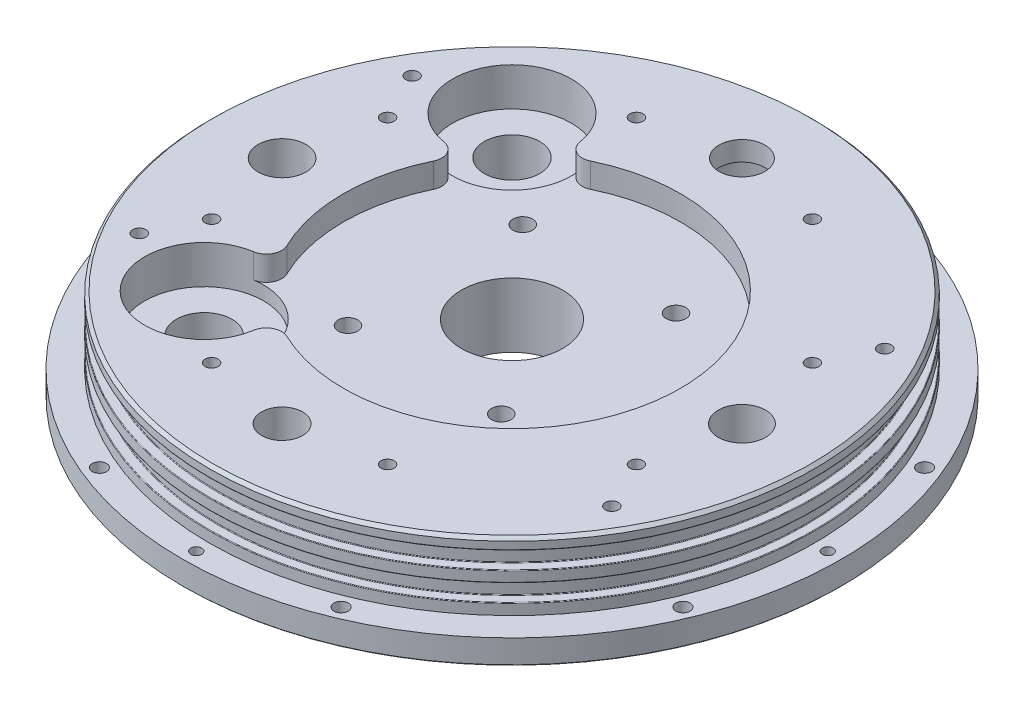
SolidWorks part; units mm, degrees
other "Markup1"
sketch "Sketch44" plane through (68.2625, -5.08, 68.2625) normal (0.274, -0.9578, 0.0865) x (-0.9537, -0.259, 0.1532)
material "6061-T6 (SS)"
ref_plane "Front Plane" through (0, 0, 0) normal (0, 0, 1) x (1, 0, 0)
ref_plane "Top Plane" through (0, 0, 0) normal (0, 1, 0) x (1, 0, 0)
ref_plane "Right Plane" through (0, 0, 0) normal (1, 0, 0) x (0, 0, -1)
ref_plane "Plane1" through (0, -5.08, 0) normal (0, -1, 0) x (1, 0, 0)
sketch "Sketch1" plane through (0, -5.08, 0) normal (0, -1, 0) x (1, 0, 0)
  circle A0 centre (0, 0) radius 68.2625
  dimension "D1" = 136.525
extrude "Boss-Extrude1" add sketch "Sketch1" against normal blind 19.05
sketch "Sketch2" plane through (0, -5.08, 0) normal (0, -1, 0) x (1, 0, 0)
  line L0 (0, 0) -> (0, -47.625) construction
  line L1 (0, 0) -> (25.4, 0) construction
  circle A0 centre (0, -47.625) radius 11.65
  dimension "D3" = 23.3
  dimension "D1" = 90
  dimension "D2" = 47.625
extrude "Cut-Extrude1" cut sketch "Sketch2" against normal blind 1.5
hole_wizard "M22x1.0 Tapped Hole2" positions "Sketch4" profile "Sketch3" tap size "M22x1.0" standard "ANSI Metric"
sketch "Sketch4" plane through (0, -3.58, 0) normal (0, -1, 0) x (-1, 0, 0)
  line L0 (0, 0) -> (0, 47.625) construction
  point P0 (0, 47.625)
  dimension "D1" = 47.625
sketch "Sketch3" plane through (0, -3.58, -47.625) normal (1, 0, 0) x (0, 0, -1)
  line L0 (0, 0) -> (0, 3.5001)
  line L1 (0, 3.5001) -> (10.325, 3.5001)
  line L2 (10.325, 3.5001) -> (10.325, 0)
  line L5 (10.325, 0) -> (0, 0)
  line L10 (0, 3.5001) -> (-10.325, 3.5001) construction
  line L11 (0, -6.35) -> (0, 107.95) construction
  dimension "Tap Drill Dia." = 20.65
  dimension "Tap Drill Depth" = 3.5001
  dimension "Drill Angle" = 180
cosmetic thread "Hole Thread16" parameters "D1"=3.5001, "D2"=22
sketch "Sketch5" plane through (0, -0.0799, 0) normal (0, -1, 0) x (1, 0, 0)
  line L0 (0, 0) -> (0, -47.625) construction
  circle A0 centre (0, -47.625) radius 10.325
  dimension "D1" = 20.65
extrude "Cut-Extrude2" cut sketch "Sketch5" against normal blind 1.4
sketch "Sketch6" plane through (0, 1.3201, 0) normal (0, -1, 0) x (1, 0, 0)
  line L0 (0, 0) -> (0, -47.625) construction
  circle A0 centre (0, -47.625) radius 9.65
  dimension "D1" = 19.3
extrude "Cut-Extrude3" cut sketch "Sketch6" against normal blind 0.9
ref_plane "Plane2" through (0, 2.22, 0) normal (0, -1, 0) x (1, 0, 0)
sketch "Sketch7" plane through (0, 2.22, 0) normal (0, -1, 0) x (1, 0, 0)
  circle A0 centre (0, -47.625) radius 10.1
  dimension "D1" = 20.2
extrude "Cut-Extrude4" cut sketch "Sketch7" against normal blind 1.2
sketch "Sketch8" plane through (0, 3.42, 0) normal (0, -1, 0) x (1, 0, 0)
  circle A0 centre (0, -47.625) radius 9.515
  dimension "D1" = 19.03
extrude "Cut-Extrude5" cut sketch "Sketch8" against normal blind 5
chamfer "Chamfer1" distance 0.4346 angle 49 1 edges at (0, 3.42, -38.11)
sketch "Sketch9" plane through (0, 8.42, 0) normal (0, -1, 0) x (1, 0, 0)
  line L0 (0, 0) -> (0, -47.625) construction
  circle A0 centre (0, -47.625) radius 7.5
  dimension "D1" = 15
extrude "Cut-Extrude6" cut sketch "Sketch9" against normal blind 1.5
ref_plane "Plane3" through (0, 0, 0) normal (-0.7071, 0, 0.7071) x (0, -1, 0)
sketch "Sketch10" plane through (0, 0, 0) normal (-0.7071, 0, 0.7071) x (0, -1, 0)
  line L0 (0, 68.3133) -> (-13.97, 68.3133)
  line L1 (-13.97, 68.3133) -> (-13.97, 62.5983)
  line L2 (-13.97, 62.5983) -> (0, 62.5983)
  line L3 (0, 62.5983) -> (0, 68.3133)
  line L4 (0, 0) -> (-13.97, 0) construction
  line L5 (-13.97, 0) -> (-13.97, 62.5983) construction
  dimension "D1" = 62.5983
  dimension "D2" = 5.715
  dimension "D3" = 13.97
  dimension "D4" = 13.97
revolve "Cut-Revolve1" cut sketch "Sketch10" angle 360 about L4
hole_wizard "#4 Clearance Hole1" positions "Sketch12" profile "Sketch11" hole size "#4" standard "ANSI Inch" end condition through all
sketch "Sketch12" plane through (0, -5.08, 0) normal (0, -1, 0) x (-1, 0, 0)
  line L0 (0, 0) -> (25.0294, -60.4263) construction
  line L2 (0, 0) -> (-25.0294, -60.4263) construction
  line L4 (0, 0) -> (-60.4263, -25.0294) construction
  line L6 (0, 0) -> (-60.4263, 25.0294) construction
  line L8 (0, 0) -> (-25.0294, 60.4263) construction
  line L10 (0, 0) -> (25.0294, 60.4263) construction
  line L12 (0, 0) -> (60.4263, 25.0294) construction
  line L14 (0, 0) -> (60.4263, -25.0294) construction
  line L16 (0, 0) -> (0, 65.405) construction
  circle A1 centre (0, 0) radius 65.405 construction
  point P0 (25.0294, -60.4263)
  point P1 (25.0294, 60.4263)
  point P2 (60.4263, -25.0294)
  point P3 (-25.0294, 60.4263)
  point P4 (-60.4263, 25.0294)
  point P5 (-60.4263, -25.0294)
  point P6 (-25.0294, -60.4263)
  point P7 (60.4263, 25.0294)
  point P57 (0, 0)
  point P58 (0, 0)
  point P59 (0, 0)
  point P60 (0, 0)
  point P61 (0, 0)
  point P62 (0, 0)
  point P63 (0, 0)
  point P64 (0, 0)
  point P65 (0, 0)
  point P66 (0, 0)
  dimension "D1" = 130.81
  dimension "D2" = 22.5
  dimension "D3" = 22.5
  dimension "D4" = 45
sketch "Sketch11" plane through (-25.0294, -5.08, 60.4263) normal (1, 0, 0) x (0, 0, -1)
  line L0 (0, 0) -> (0, 19.05)
  line L1 (0, 19.05) -> (1.4732, 19.05)
  line L2 (1.4732, 19.05) -> (1.4732, 0)
  line L5 (1.4732, 0) -> (0, 0)
  line L11 (0, -6.35) -> (0, 107.95) construction
  dimension "Thru Hole Dia." = 2.9464
  dimension "Thru Hole Depth" = 19.05
hole_wizard "#4-40 Tapped Hole1" positions "Sketch14" profile "Sketch13" tap size "#4-40" standard "ANSI Inch" end condition through all
sketch "Sketch14" plane through (0, -5.08, 0) normal (0, -1, 0) x (-1, 0, 0)
  line L0 (0, 0) -> (0, 65.405) construction
  line L2 (0, 0) -> (65.405, 0) construction
  line L3 (0, 0) -> (0, -65.405) construction
  line L4 (0, 0) -> (-65.405, 0) construction
  circle A0 centre (0, 0) radius 65.405 construction
  point P0 (0, -65.405)
  point P1 (0, 65.405)
  point P2 (-65.405, 0)
  point P3 (65.405, 0)
  point P20 (0, 0)
  point P21 (0, 0)
  point P22 (0, 0)
  point P23 (0, 0)
  point P24 (0, 0)
  point P25 (0.0664, 65.405)
  point P26 (0.1049, 65.405)
  point P27 (0, 0)
  point P28 (0, 0)
  point P29 (0, 0)
  point P30 (0.0003, 65.405)
  point P31 (0.0019, 65.405)
  point P32 (0, 65.405)
  point P33 (0, 0)
  point P34 (0, 0)
  point P35 (0, 65.405)
  dimension "D2" = 130.81
  dimension "D1" = 4
sketch "Sketch13" plane through (0, -5.08, 65.405) normal (1, 0, 0) x (0, 0, -1)
  line L0 (0, 0) -> (0, 19.05)
  line L1 (0, 19.05) -> (1.1303, 19.05)
  line L2 (1.1303, 19.05) -> (1.1303, 0)
  line L5 (1.1303, 0) -> (0, 0)
  line L11 (0, -6.35) -> (0, 107.95) construction
  dimension "Thru Tap Drill Dia." = 2.2606
  dimension "Thru Tap Drill Depth" = 19.05
cosmetic thread "Hole Thread21" parameters "D2"=2.8448
cosmetic thread "Hole Thread22" parameters "D2"=2.8448
cosmetic thread "Hole Thread23" parameters "D2"=2.8448
cosmetic thread "Hole Thread24" parameters "D2"=2.8448
hole_wizard "Hole2" positions "Sketch16" profile "Sketch15" legacy end condition through all
sketch "Sketch16" plane through (0, 9.92, 0) normal (0, -1, 0) x (-1, 0, 0)
  line L0 (0, 0) -> (0, 47.625) construction
  point P0 (0, 47.625)
sketch "Sketch15" plane through (0, 9.92, -47.625) normal (1, 0, 0) x (0, 0, -1)
  line L0 (0, 0) -> (0, 4.05)
  line L1 (0, 4.05) -> (4.75, 4.05)
  line L2 (4.75, 4.05) -> (4.75, 0)
  line L3 (4.75, 0) -> (0, 0)
  line L4 (0, 110) -> (0, -10) construction
  dimension "Diameter" = 9.5
  dimension "Depth" = 4.05
sketch "Sketch40" plane through (0, 13.97, 0) normal (0, 1, 0) x (1, 0, 0)
  line L0 (0, 0) -> (-56.515, 0) construction
  line L1 (48.9434, -28.2575) -> (-48.9434, 28.2575)
  line L2 (-48.9434, -28.2575) -> (48.9434, 28.2575)
  circle A0 centre (0, 0) radius 56.515
  point P7 (0, 0)
  point P10 (0, 0)
  dimension "D1" = 113.03
  dimension "D2" = 30
  dimension "D3" = 30
hole_wizard "M10x1.5 Tapped Hole2" positions "Sketch22" profile "Sketch21" tap size "M10x1.5" standard "ANSI Metric" end condition up to next
sketch "Sketch22" plane through (0, -5.08, 0) normal (0, -1, 0) x (-1, 0, 0)
  line L0 (0, 0) -> (0, -47.625)
  point P0 (0, -47.625)
  dimension "D1" = 47.625
cosmetic thread "Hole Thread13" parameters "D2"=10
sketch "Sketch21" plane through (0, -5.08, 47.625) normal (1, 0, 0) x (0, 0, -1)
  line L0 (0, 0) -> (0, 19.05)
  line L1 (0, 19.05) -> (4.25, 19.05)
  line L2 (4.25, 19.05) -> (4.25, 0)
  line L5 (4.25, 0) -> (0, 0)
  line L11 (0, -6.35) -> (0, 107.95) construction
  dimension "Thru Tap Drill Dia." = 8.5
  dimension "Thru Tap Drill Depth" = 19.05
hole_wizard "Hole4" positions "Sketch24" profile "Sketch23" legacy end condition through all
sketch "Sketch24" plane through (0, -5.08, 0) normal (0, -1, 0) x (-1, 0, 0)
  line L0 (0, 0) -> (-47.625, 0)
  point P0 (-47.625, 0)
  dimension "D1" = 47.625
sketch "Sketch23" plane through (47.625, -5.08, 0) normal (1, 0, 0) x (0, 0, -1)
  line L0 (0, 0) -> (0, 19.05)
  line L1 (0, 19.05) -> (4.9, 19.05)
  line L2 (4.9, 19.05) -> (4.9, 0)
  line L3 (4.9, 0) -> (0, 0)
  line L4 (0, 110) -> (0, -10) construction
  dimension "Diameter" = 9.8
  dimension "Depth" = 19.05
hole_wizard "7/8-20 Tapped Hole1" positions "Sketch26" profile "Sketch25" tap size "7/8-20" standard "ANSI Inch" end condition up to next
sketch "Sketch26" plane through (0, -5.08, 0) normal (0, -1, 0) x (-1, 0, 0)
  point P0 (0, 0)
cosmetic thread "Hole Thread14" parameters "D2"=22.225
sketch "Sketch25" plane through (0, -5.08, 0) normal (1, 0, 0) x (0, 0, -1)
  line L0 (0, 0) -> (0, 19.05)
  line L1 (0, 19.05) -> (10.4902, 19.05)
  line L2 (10.4902, 19.05) -> (10.4902, 0)
  line L5 (10.4902, 0) -> (0, 0)
  line L11 (0, -6.35) -> (0, 107.95) construction
  dimension "Thru Tap Drill Dia." = 20.9804
  dimension "Thru Tap Drill Depth" = 19.05
hole_wizard "7/16-20 Tapped Hole1" positions "Sketch28" profile "Sketch27" tap size "7/16-20" standard "ANSI Inch" end condition through all
sketch "Sketch28" plane through (0, -5.08, 0) normal (0, -1, 0) x (-1, 0, 0)
  line L0 (0, 0) -> (47.625, 0) construction
  point P0 (47.625, 0)
  dimension "D1" = 47.625
sketch "Sketch27" plane through (-47.625, -5.08, 0) normal (1, 0, 0) x (0, 0, -1)
  line L0 (0, 0) -> (0, 19.05)
  line L1 (0, 19.05) -> (4.9606, 19.05)
  line L2 (4.9606, 19.05) -> (4.9606, 0)
  line L5 (4.9606, 0) -> (0, 0)
  line L11 (0, -6.35) -> (0, 107.95) construction
  dimension "Thru Tap Drill Dia." = 9.9212
  dimension "Thru Tap Drill Depth" = 19.05
cosmetic thread "Hole Thread15" parameters "D2"=11.1125
hole_wizard "7/16 Clearance Hole1" positions "Sketch30" profile "Sketch29" hole size "7/16" standard "ANSI Inch" end condition through all
sketch "Sketch30" plane through (0, 13.97, 0) normal (0, 1, 0) x (1, 0, 0)
  line L0 (0, 0) -> (-31.8799, 31.8799)
  line L2 (0, 0) -> (-31.8799, -31.8799)
  line L4 (0, 0) -> (-45.085, 0)
  point P0 (-31.8799, 31.8799)
  point P1 (-31.8799, -31.8799)
  dimension "D1" = 45.085
  dimension "D2" = 90
  dimension "D3" = 45
sketch "Sketch29" plane through (-31.8799, 13.97, -31.8799) normal (1, 0, 0) x (0, 0, 1)
  line L0 (0, 0) -> (0, 19.05)
  line L1 (0, 19.05) -> (5.755, 19.05)
  line L2 (5.755, 19.05) -> (5.755, 0)
  line L5 (5.755, 0) -> (0, 0)
  line L11 (0, -6.35) -> (0, 107.95) construction
  dimension "Thru Hole Dia." = 11.51
  dimension "Thru Hole Depth" = 19.05
sketch "Sketch31" plane through (0, 13.97, 0) normal (0, 1, 0) x (-1, 0, 0)
  line L0 (31.8799, -31.8799) -> (0, 0) construction
  line L1 (0, 0) -> (31.8799, 31.8799) construction
  line L2 (0, 0) -> (47.625, 0) construction
  circle A1 centre (31.8799, -31.8799) radius 12.319
  circle A2 centre (31.8799, 31.8799) radius 5.755 construction
  circle A3 centre (31.8799, 31.8799) radius 12.319
  circle A4 centre (31.8799, -31.8799) radius 5.755 construction
  dimension "D1" = 24.638
  dimension "D2" = 24.638
extrude "Cut-Extrude7" cut sketch "Sketch31" against normal blind 7.9375
sketch "Sketch32" plane through (0, -5.08, 0) normal (0, -1, 0) x (1, 0, 0)
  line L0 (0, 0) -> (47.625, 0) construction
  circle A0 centre (47.625, 0) radius 4.7625
  circle A1 centre (47.625, 0) radius 7.1374
  dimension "D1" = 14.2748
  dimension "D2" = 9.525
  dimension "D3" = 47.625
extrude "Cut-Extrude8" cut sketch "Sketch32" against normal blind 7.62
sketch "Sketch33" plane through (0, -5.08, 0) normal (0, -1, 0) x (1, 0, 0)
  line L0 (47.625, 0) -> (0, 0) construction
  line L2 (-31.8799, 31.8799) -> (0, 0) construction
  line L3 (0, 0) -> (-47.625, 0) construction
  line L4 (-31.8799, -31.8799) -> (0, 0) construction
  line L5 (0, 0) -> (0, 47.625) construction
  circle A0 centre (47.625, 0) radius 6.35
  circle A1 centre (47.625, 0) radius 13.6525
  circle A2 centre (0, 47.625) radius 2.54
  circle A3 centre (0, 47.625) radius 11.1125
  circle A4 centre (-31.8799, -31.8799) radius 5.08
  circle A5 centre (-31.8799, -31.8799) radius 10.4775
  circle A6 centre (-47.625, 0) radius 4.7625
  circle A7 centre (-47.625, 0) radius 15.24
  circle A8 centre (-31.8799, 31.8799) radius 5.08
  circle A9 centre (-31.8799, 31.8799) radius 10.4775
  circle A10 centre (0, 0) radius 5.7341
  circle A11 centre (0, 0) radius 24.4475
  circle A12 centre (0, 0) radius 47.625 construction
  dimension "D1" = 27.305
  dimension "D2" = 48.895
  dimension "D3" = 20.955
  dimension "D4" = 30.48
  dimension "D5" = 20.955
  dimension "D6" = 22.225
  dimension "D7" = 95.25
  dimension "D11" = 5.08
  dimension "D12" = 10.16
  dimension "D13" = 9.525
  dimension "D14" = 10.16
  dimension "D15" = 11.4681
  dimension "D16" = 12.7
  dimension "D8" = 45
  dimension "D9" = 45
  dimension "D10" = 47.625
  dimension "D17" = 45.085
  dimension "D18" = 45.085
extrude "Cut-Extrude9" cut sketch "Sketch33" against normal blind 0.635
chamfer "Chamfer2" distance 0.4346 angle 49 1 edges at (0, 1.3201, -37.975)
chamfer "Chamfer3" distance 0.635 angle 15 1 edges at (47.625, -4.445, 7.1374)
sketch "Sketch34" plane through (0, -4.445, 0) normal (0, -1, 0) x (1, 0, 0)
  line L0 (47.625, 0) -> (59.625, 0) construction
  circle A0 centre (59.625, 0) radius 0.8509
  dimension "D1" = 1.7018
  dimension "D2" = 12
extrude "Cut-Extrude10" cut sketch "Sketch34" against normal blind 3.365
ref_plane "Plane4" through (0, 0, 0) normal (0, 0, -1) x (-1, 0, 0)
ref_plane "Plane5" through (0, 0, 0) normal (0.7071, 0, -0.7071) x (0, 1, 0)
sketch "Sketch38" plane through (0, 0, 0) normal (0.7071, 0, -0.7071) x (0, 1, 0)
  line L0 (11.684, 62.6745) -> (8.128, 62.6745)
  line L1 (8.128, 62.6745) -> (8.128, 60.6425)
  line L2 (8.128, 60.6425) -> (11.684, 60.6425)
  line L3 (11.684, 60.6425) -> (11.684, 62.6745)
  line L4 (8.128, 0) -> (11.684, 0) construction
  line L5 (11.684, 60.6425) -> (11.684, 0) construction
  line L6 (0, 0) -> (8.128, 0) construction
  dimension "D1" = 2.032
  dimension "D2" = 3.556
  dimension "D3" = 60.6425
  dimension "D4" = 3.556
  dimension "D5" = 8.128
revolve "Cut-Revolve4" cut sketch "Sketch38" angle 360 about L4
sketch "Sketch39" plane through (0, 0, 0) normal (-0.7071, 0, 0.7071) x (0, -1, 0)
  line L0 (-2.286, 62.6745) -> (-5.842, 62.6745)
  line L1 (-5.842, 62.6745) -> (-5.842, 60.6425)
  line L2 (-5.842, 60.6425) -> (-2.286, 60.6425)
  line L3 (-2.286, 60.6425) -> (-2.286, 62.6745)
  line L4 (-2.286, 0) -> (-5.842, 0) construction
  line L5 (-5.842, 0) -> (-5.842, 60.6425) construction
  line L6 (-2.286, 0) -> (0, 0) construction
  dimension "D1" = 3.556
  dimension "D2" = 60.6425
  dimension "D3" = 2.032
  dimension "D4" = 2.286
  dimension "D5" = 3.556
revolve "Cut-Revolve5" cut sketch "Sketch39" angle 360 about L4
fillet "Fillet2" radius 0.127 8 edges at (0, 8.128, -62.5983) (0, 5.842, 60.6425) (0, 2.286, 60.6425) (0, 11.684, 60.6425) (0, 5.842, -62.5983) (0, 2.286, 62.5983) (0, 8.128, 60.6425) (0, 11.684, 62.5983)
chamfer "Chamfer4" distance 0.254 angle 45 1 edges at (0, -5.08, 68.2625)
hole_wizard "#6-32 Tapped Hole2" positions "Sketch41" profile "Sketch42" tap size "#6-32" standard "ANSI Inch"
sketch "Sketch41" plane through (0, 13.97, 0) normal (0, 1, 0) x (1, 0, 0)
  point P0 (-48.9434, 28.2575)
  point P3 (-48.9434, -28.2575)
  point P6 (48.9434, -28.2575)
  point P9 (48.9434, 28.2575)
sketch "Sketch42" plane through (-48.9434, 13.97, -28.2575) normal (1, 0, 0) x (0, 0, 1)
  line L0 (0, 0) -> (0, 10.8101)
  line L1 (0, 10.8101) -> (1.3525, 9.9974)
  line L2 (1.3525, 9.9974) -> (1.3525, 0)
  line L5 (1.3525, 0) -> (0, 0)
  line L10 (0, 10.8101) -> (-1.3526, 9.9974) construction
  line L11 (0, -6.35) -> (0, 107.95) construction
  dimension "Tap Drill Dia." = 2.7051
  dimension "Tap Drill Depth" = 9.9974
  dimension "Drill Angle" = 118
cosmetic thread "Hole Thread17" parameters "D1"=7.62, "D2"=3.5052
cosmetic thread "Hole Thread18" parameters "D1"=7.62, "D2"=3.5052
cosmetic thread "Hole Thread19" parameters "D1"=7.62, "D2"=3.5052
cosmetic thread "Hole Thread20" parameters "D1"=7.62, "D2"=3.5052
sketch "Sketch43" plane through (0, 13.97, 0) normal (0, 1, 0) x (1, 0, 0)
  circle A0 centre (0, 0) radius 34.925
  circle A1 centre (-48.9434, 28.2575) radius 4.7625 construction
  circle A2 centre (-48.9434, -28.2575) radius 4.7625 construction
  circle A3 centre (48.9434, -28.2575) radius 4.7625 construction
  circle A4 centre (48.9434, 28.2575) radius 4.7625 construction
  circle A5 centre (0, 47.625) radius 12.7 construction
  circle A6 centre (-47.625, 0) radius 11.1125 construction
  circle A7 centre (0, -47.625) radius 11.1125 construction
  circle A8 centre (47.625, 0) radius 11.1125 construction
  dimension "D1" = 22.225
  dimension "D2" = 25.4
  dimension "D3" = 9.525
  dimension "D4" = 69.85
extrude "Cut-Extrude13" cut sketch "Sketch43" against normal blind 5.08
hole_wizard "#6-32 Tapped Hole1" positions "Sketch18" profile "Sketch17" tap size "#6-32" standard "ANSI Inch"
sketch "Sketch18" plane through (0, 13.97, 0) normal (0, 1, 0) x (1, 0, 0)
  line L0 (0, 0) -> (18.2253, 43.9998) construction
  line L2 (0, 0) -> (-18.2253, 43.9998) construction
  line L4 (0, 0) -> (0, 47.625) construction
  line L5 (0, 0) -> (18.2253, -43.9998) construction
  line L7 (0, 0) -> (-18.2253, -43.9998) construction
  line L8 (0, 0) -> (-43.9998, -18.2253) construction
  line L10 (0, 0) -> (-43.9998, 18.2253) construction
  line L13 (43.9998, 18.2253) -> (0, 0) construction
  line L14 (0, 0) -> (43.9998, -18.2253) construction
  line L15 (0, 0) -> (-47.625, 0) construction
  circle A0 centre (0, 0) radius 47.625 construction
  point P0 (18.2253, -43.9998)
  point P1 (43.9998, 18.2253)
  point P2 (-43.9998, 18.2253)
  point P3 (18.2253, 43.9998)
  point P4 (-18.2253, 43.9998)
  point P5 (-18.2253, -43.9998)
  point P6 (-43.9998, -18.2253)
  point P7 (43.9998, -18.2253)
  dimension "D1" = 95.25
  dimension "D2" = 45
  dimension "D3" = 22.5
  dimension "D4" = 45
  dimension "D5" = 45
  dimension "D6" = 45
  dimension "D7" = 22.5
sketch "Sketch17" plane through (18.2253, 13.97, 43.9998) normal (1, 0, 0) x (0, 0, 1)
  line L0 (0, 0) -> (0, 9.9974)
  line L1 (0, 9.9974) -> (1.3525, 9.1847)
  line L2 (1.3525, 9.1847) -> (1.3525, 0)
  line L5 (1.3525, 0) -> (0, 0)
  line L10 (0, 9.9974) -> (-1.3526, 9.1847) construction
  line L11 (0, -6.35) -> (0, 107.95) construction
  dimension "Tap Drill Dia." = 2.7051
  dimension "Tap Drill Depth" = 9.9974
  dimension "Drill Angle" = 118
cosmetic thread "Hole Thread1" parameters "D1"=7.62, "D2"=3.5052
cosmetic thread "Hole Thread2" parameters "D1"=7.62, "D2"=3.5052
cosmetic thread "Hole Thread3" parameters "D1"=7.62, "D2"=3.5052
cosmetic thread "Hole Thread4" parameters "D1"=7.62, "D2"=3.5052
cosmetic thread "Hole Thread5" parameters "D1"=7.62, "D2"=3.5052
cosmetic thread "Hole Thread6" parameters "D1"=7.62, "D2"=3.5052
cosmetic thread "Hole Thread7" parameters "D1"=7.62, "D2"=3.5052
cosmetic thread "Hole Thread8" parameters "D1"=7.62, "D2"=3.5052
hole_wizard "#10-32 Tapped Hole1" positions "Sketch20" profile "Sketch19" tap size "#10-32" standard "ANSI Inch"
sketch "Sketch20" plane through (0, 8.89, 0) normal (0, 1, 0) x (1, 0, 0)
  line L0 (15.875, 18.0975) -> (-15.875, -18.0975) construction
  line L2 (15.875, -18.0975) -> (-15.875, 18.0975) construction
  line L4 (0, 0) -> (0, 24.0735) construction
  line L5 (-15.875, 18.0975) -> (15.875, 18.0975) construction
  line L7 (-15.875, 18.0975) -> (-15.875, -18.0975) construction
  circle A0 centre (0, 0) radius 24.0735 construction
  point P0 (15.875, 18.0975)
  point P1 (-15.875, -18.0975)
  point P2 (-15.875, 18.0975)
  point P3 (15.875, -18.0975)
  dimension "D1" = 31.75
  dimension "D2" = 36.195
sketch "Sketch19" plane through (15.875, 8.89, -18.0975) normal (1, 0, 0) x (0, 0, 1)
  line L0 (0, 0) -> (0, 10.7383)
  line L1 (0, 10.7383) -> (2.0193, 9.525)
  line L2 (2.0193, 9.525) -> (2.0193, 0)
  line L5 (2.0193, 0) -> (0, 0)
  line L10 (0, 10.7383) -> (-2.0193, 9.525) construction
  line L11 (0, -6.35) -> (0, 107.95) construction
  dimension "Tap Drill Dia." = 4.0386
  dimension "Tap Drill Depth" = 9.525
  dimension "Drill Angle" = 118
cosmetic thread "Hole Thread9" parameters "D1"=7.9375, "D2"=4.826
cosmetic thread "Hole Thread10" parameters "D1"=7.9375, "D2"=4.826
cosmetic thread "Hole Thread11" parameters "D1"=7.9375, "D2"=4.826
cosmetic thread "Hole Thread12" parameters "D1"=7.9375, "D2"=4.826
fillet "Fillet4" radius 3.175 4 edges at (-19.9962, 11.43, 28.634) (-28.634, 11.43, 19.9962) (-19.9962, 11.43, -28.634) (-28.634, 11.43, -19.9962)
chamfer "Chamfer5" distance 0.635 angle 45 1 edges at (0, 13.97, 62.5983)
